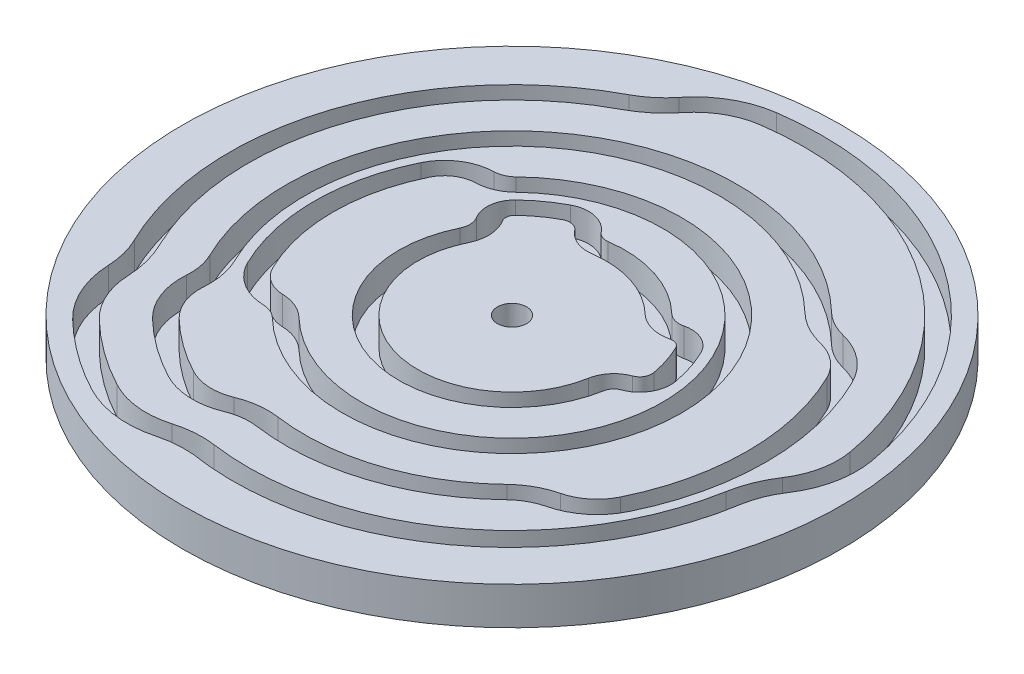
SolidWorks part; units mm, degrees
ref_plane "前视基准面" through (0, 0, 0) normal (0, 0, 1) x (1, 0, 0)
ref_plane "上视基准面" through (0, 0, 0) normal (0, 1, 0) x (1, 0, 0)
ref_plane "右视基准面" through (0, 0, 0) normal (1, 0, 0) x (0, 0, -1)
sketch "草图1" plane through (0, 0, 0) normal (0, 1, 0) x (1, 0, 0)
  line L0 (0, 0) -> (35, 0) construction
  line L1 (0, 0) -> (28.3156, -20.5725) construction
  line L2 (0, 0) -> (10.8156, -33.287) construction
  line L3 (0, 0) -> (-10.8156, -33.287) construction
  line L4 (0, 0) -> (-28.3156, -20.5725) construction
  line L5 (0, 0) -> (-35, 0) construction
  line L6 (0, 0) -> (-28.3156, 20.5725) construction
  line L7 (0, 0) -> (-10.8156, 33.287) construction
  line L8 (0, 0) -> (10.8156, 33.287) construction
  line L9 (0, 0) -> (28.3156, 20.5725) construction
  line L10 (0, 0) -> (34.4683, -6.0777) construction
  line L11 (0, 0) -> (14.7721, 2.6047) construction
  line L12 (0, 0) -> (10.4199, 10.7901) construction
  line L13 (0, 0) -> (13.4819, 6.5756) construction
  line L14 (0, 0) -> (-4.8711, 34.6594) construction
  line L15 (0, 0) -> (-7.0421, 13.2442) construction
  line L16 (0, 0) -> (-13.4819, 6.5756) construction
  line L17 (0, 0) -> (-10.4199, 10.7901) construction
  line L18 (-10.4199, 10.7901) -> (-24.313, 25.1769) construction
  line L19 (-13.4819, 6.5756) -> (-31.4578, 15.343) construction
  line L20 (-13.4819, -6.5756) -> (-31.4578, -15.343) construction
  line L21 (-10.4199, -10.7901) -> (-24.313, -25.1769) construction
  line L22 (0, 0) -> (-20.6079, -38.7578) construction
  line L23 (0, 0) -> (-5.3411, -38.0037) construction
  line L24 (0.985, -1.02) -> (31.4061, -32.522) construction
  line L25 (0, 0) -> (40.0534, -19.5353) construction
  circle A0 centre (0, 0) radius 35 construction
  circle A1 centre (0, 0) radius 10 construction
  circle A2 centre (0, 0) radius 15 construction
  circle A3 centre (0, 0) radius 12 construction
  arc A4 (12.8025, 2.2574) -> (11.6843, 5.6988) centre (0, 0) ccw
  arc A5 (9.8481, -1.7365) -> (11.9726, 0.8104) centre (13.1308, -2.3153) cw
  arc A6 (11.9726, 0.8104) -> (12.8025, 2.2574) centre (11.5202, 2.0313) ccw
  arc A7 (11.8177, -2.0838) -> (12.6675, -1.065) centre (13.1308, -2.3153) cw
  arc A8 (12.6675, -1.065) -> (14.7721, 2.6047) centre (11.5202, 2.0313) ccw
  circle A9 centre (0, 0) radius 13 construction
  arc A10 (13.4819, 6.5756) -> (14.7721, 2.6047) centre (0, 0) cw
  arc A11 (-1.3917, 9.9027) -> (-4.4704, 11.1362) centre (-1.8556, 13.2036) cw
  arc A12 (-4.4704, 11.1362) -> (-6.1031, 11.4783) centre (-5.4918, 10.3286) ccw
  arc A13 (6.9466, 7.1934) -> (10.6059, 6.2045) centre (9.6728, 10.0164) ccw
  arc A14 (8.3359, 8.6321) -> (10.1304, 8.1471) centre (9.6728, 10.0164) ccw
  arc A15 (10.1304, 8.1471) -> (13.4819, 6.5756) centre (10.8315, 5.2829) cw
  arc A16 (10.6059, 6.2045) -> (11.6843, 5.6988) centre (10.8315, 5.2829) cw
  arc A17 (-2.9016, 12.3766) -> (-7.0421, 13.2442) centre (-5.4918, 10.3286) ccw
  arc A18 (-1.6701, 11.8832) -> (-2.9016, 12.3766) centre (-1.8556, 13.2036) cw
  arc A19 (-1.3917, 9.9027) -> (6.9466, 7.1934) centre (0, 0) cw
  arc A20 (-1.6701, 11.8832) -> (8.3359, 8.6321) centre (0, 0) cw
  arc A21 (-6.1031, 11.4783) -> (-9.0306, 9.3514) centre (0, 0) ccw
  arc A22 (-10.4199, 10.7901) -> (-7.0421, 13.2442) centre (0, 0) cw
  arc A23 (-9.1782, 8.1695) -> (-9.0306, 9.3514) centre (-8.3714, 8.6689) cw
  arc A24 (-10.8788, 7.1169) -> (-10.4199, 10.7901) centre (-8.3714, 8.6689) cw
  arc A25 (-8.9879, 4.3837) -> (-9.1782, 8.1695) centre (-12.5152, 6.1041) ccw
  arc A26 (-10.7855, 5.2605) -> (-10.8788, 7.1169) centre (-12.5152, 6.1041) ccw
  arc A27 (-8.9879, 4.3837) -> (9.8481, -1.7365) centre (0, 0) ccw
  arc A28 (-10.7855, 5.2605) -> (11.8177, -2.0838) centre (0, 0) ccw
  circle A29 centre (0, 0) radius 16 construction
  circle A30 centre (0, 0) radius 18 construction
  circle A31 centre (0, 0) radius 19 construction
  circle A32 centre (0, 0) radius 21 construction
  arc A33 (-12.5039, 12.9481) -> (-14.1657, 12.2475) centre (-14.2408, 14.7467) cw
  arc A34 (-14.1657, 12.2475) -> (-18.8747, 9.2058) centre (-14.003, 6.8297) ccw
  arc A35 (-11.1145, 11.5094) -> (-14.1057, 10.2484) centre (-14.2408, 14.7467) cw
  arc A36 (-14.1057, 10.2484) -> (-17.0771, 8.3291) centre (-14.003, 6.8297) ccw
  arc A37 (-18.8747, -9.2058) -> (-18.8747, 9.2058) centre (0, 0) cw
  arc A38 (-17.0771, -8.3291) -> (-17.0771, 8.3291) centre (0, 0) cw
  arc A39 (-11.1145, -11.5094) -> (-11.1145, 11.5094) centre (0, 0) ccw
  arc A40 (-12.5039, -12.9481) -> (-12.5039, 12.9481) centre (0, 0) ccw
  arc A41 (-14.1057, -10.2484) -> (-17.0771, -8.3291) centre (-14.003, -6.8297) cw
  arc A42 (-11.1145, -11.5094) -> (-14.1057, -10.2484) centre (-14.2408, -14.7467) ccw
  arc A43 (-12.5039, -12.9481) -> (-14.1657, -12.2475) centre (-14.2408, -14.7467) ccw
  arc A44 (-14.1657, -12.2475) -> (-18.8747, -9.2058) centre (-14.003, -6.8297) cw
  arc A45 (-14.1057, -10.2484) -> (-13.1985, -13.6675) centre (-10.8226, -11.2072) ccw [skipped]
  arc A46 (-14.3807, -7.0139) -> (-14.1057, -10.2484) centre (-18.4256, -8.9868) cw [skipped]
  arc A47 (-16.1783, -7.8907) -> (-16.0255, -9.6877) centre (-18.4256, -8.9868) cw [skipped]
  arc A48 (-16.0255, -9.6877) -> (-14.5878, -15.1061) centre (-10.8226, -11.2072) ccw [skipped]
  circle A49 centre (0, 0) radius 22 construction
  circle A50 centre (0, 0) radius 24 construction
  circle A51 centre (0, 0) radius 25 construction
  circle A52 centre (0, 0) radius 27 construction
  arc A53 (24.2674, 11.836) -> (19.4142, 15.7508) centre (17.6639, 8.6153) ccw
  arc A54 (19.4142, 15.7508) -> (16.6718, 17.2642) centre (20.8456, 21.5862) cw
  arc A55 (22.4699, 10.9593) -> (18.9378, 13.8084) centre (17.6639, 8.6153) ccw
  arc A56 (18.9378, 13.8084) -> (15.2825, 15.8255) centre (20.8456, 21.5862) cw
  arc A57 (-6.4483, -24.1541) -> (-3.3402, -23.7664) centre (-4.1764, -29.7163) cw
  arc A58 (-7.2046, -22.3026) -> (-3.0618, -21.7859) centre (-4.1764, -29.7163) cw
  arc A59 (-12.6757, -23.8396) -> (-6.4483, -24.1541) centre (-9.2265, -17.3525) ccw
  arc A60 (-11.7368, -22.0737) -> (-7.2046, -22.3026) centre (-9.2265, -17.3525) ccw
  arc A61 (-20.9792, -13.5967) -> (-21.5711, -10.5209) centre (-26.9714, -13.1548) ccw
  arc A62 (-18.9847, -13.7438) -> (-19.7735, -9.6442) centre (-26.9714, -13.1548) ccw
  arc A63 (-18.7558, -19.4222) -> (-20.9792, -13.5967) centre (-13.6521, -14.1371) cw
  arc A64 (-17.3665, -17.9835) -> (-18.9847, -13.7438) centre (-13.6521, -14.1371) cw
  arc A65 (15.2825, -15.8255) -> (18.9378, -13.8084) centre (20.8456, -21.5862) cw
  arc A66 (18.9378, -13.8084) -> (22.4699, -10.9593) centre (17.6639, -8.6153) ccw
  arc A67 (19.4142, -15.7508) -> (16.6718, -17.2642) centre (20.8456, -21.5862) ccw
  arc A68 (24.2674, -11.836) -> (19.4142, -15.7508) centre (17.6639, -8.6153) cw
  arc A69 (-21.5711, -10.5209) -> (16.6718, 17.2642) centre (0, 0) cw
  arc A70 (-11.7368, -22.0737) -> (-17.3665, -17.9835) centre (0, 0) cw
  arc A71 (-12.6757, -23.8396) -> (-18.7558, -19.4222) centre (0, 0) cw
  arc A72 (15.2825, 15.8255) -> (-19.7735, -9.6442) centre (0, 0) ccw
  arc A73 (15.2825, -15.8255) -> (-3.0618, -21.7859) centre (0, 0) cw
  arc A74 (16.6718, -17.2642) -> (-3.3402, -23.7664) centre (0, 0) cw
  arc A75 (22.4699, -10.9593) -> (22.4699, 10.9593) centre (0, 0) ccw
  arc A76 (24.2674, -11.836) -> (24.2674, 11.836) centre (0, 0) ccw
  circle A77 centre (0, 0) radius 35
  circle A78 centre (0, 0) radius 30 construction
  circle A79 centre (0, 0) radius 28 construction
  circle A80 centre (0, 0) radius 31 construction
  circle A81 centre (0, 0) radius 33 construction
  arc A82 (27.5746, -4.8621) -> (29.2876, -0.5734) centre (38.7201, -6.8274) cw
  arc A83 (29.2876, -0.5734) -> (30.529, 5.3831) centre (22.4519, 3.9589) ccw
  arc A84 (29.5442, -5.2094) -> (30.9545, -1.6786) centre (38.7201, -6.8274) cw
  arc A85 (30.9545, -1.6786) -> (32.4987, 5.7304) centre (22.4519, 3.9589) ccw
  arc A86 (-13.1452, 24.7225) -> (-9.5957, 27.677) centre (-18.4584, 34.7153) ccw
  arc A87 (-9.5957, 27.677) -> (-4.3144, 30.6983) centre (-3.1729, 22.5764) cw
  arc A88 (-4.5927, 32.6788) -> (-11.1619, 28.9208) centre (-3.1729, 22.5764) ccw
  arc A89 (-11.1619, 28.9208) -> (-14.0841, 26.4884) centre (-18.4584, 34.7153) cw
  arc A90 (-25.1662, -12.2744) -> (-24.0312, -16.7509) centre (-35.3383, -17.2356) cw
  arc A91 (-24.0312, -16.7509) -> (-21.5344, -22.2995) centre (-15.837, -16.3997) ccw
  arc A92 (-26.0294, -16.8366) -> (-26.9638, -13.1511) centre (-35.3383, -17.2356) ccw
  arc A93 (-26.0294, -16.8366) -> (-22.9237, -23.7382) centre (-15.837, -16.3997) ccw
  arc A94 (-15.4926, -29.1373) -> (-7.7363, -30.0191) centre (-10.4958, -19.7398) ccw
  arc A95 (-7.7363, -30.0191) -> (-4.1764, -29.7163) centre (-5.1119, -39.7953) cw
  arc A96 (-14.5536, -27.3714) -> (-8.0585, -28.0323) centre (-10.4958, -19.7398) ccw
  arc A97 (-8.0585, -28.0323) -> (-3.8968, -27.7275) centre (-5.2721, -37.5129) cw
  arc A98 (-3.8968, -27.7275) -> (27.5746, -4.8621) centre (0, 0) ccw
  arc A99 (29.5442, -5.2094) -> (-4.1764, -29.7163) centre (0.4305, -0.6026) cw
  arc A100 (-14.5536, -27.3714) -> (-21.5344, -22.2995) centre (0, 0) cw
  arc A101 (-15.4926, -29.1373) -> (-22.9237, -23.7382) centre (0, 0) cw
  arc A102 (-25.1662, -12.2744) -> (-13.1452, 24.7225) centre (0, 0) cw
  arc A103 (-26.9638, -13.1511) -> (-14.0841, 26.4884) centre (0, 0) cw
  arc A104 (-4.5927, 32.6788) -> (32.4987, 5.7304) centre (0, 0) cw
  arc A105 (-4.3144, 30.6983) -> (30.529, 5.3831) centre (0, 0) cw
  text T0 "             1" font "汉仪长仿宋体" height 3.5
  text T1 "  2" font "汉仪长仿宋体" height 3.5
  text T2 "         3" font "汉仪长仿宋体" height 3.5
  text T3 "         4" font "汉仪长仿宋体" height 3.5
  text T4 "   5         " font "汉仪长仿宋体" height 3.5
  text T5 "6                "
  text T6 "7                 "
  text T7 "8                 "
  text T8 "9              \r\n\r\n\r\n\r\n" font "汉仪长仿宋体" height 3.5
  text T9 "0 "
  point P17 (0, 0)
  point P19 (9.8481, -1.7365)
  point P21 (12.8025, 2.2574)
  point P27 (11.8177, -2.0838)
  point P29 (14.7721, 2.6047)
  point P48 (0, 0)
  point P55 (0, 0)
  point P69 (0, 0)
  point P95 (0, 0)
  point P135 (0, 0)
  point P147 (0, 0)
  point P160 (-0.1247, 0.6846)
  dimension "D1" = 70
  dimension "D2" = 20
  dimension "D4" = 30
  dimension "D6" = 24
  dimension "D7" = 2
  dimension "D12" = 1
  dimension "D13" = 2
  dimension "D14" = 1
  dimension "D15" = 2
  dimension "D19" = 1
  dimension "D20" = 2
  dimension "D21" = 1
  dimension "D22" = 2
  dimension "D28" = 1
  dimension "D29" = 2
  dimension "D5" = 10
  dimension "D8" = 10
  dimension "D9" = 10
  dimension "D10" = 10
  dimension "D16" = 10
  dimension "D18" = 10
  dimension "D24" = 10
  dimension "D25" = 10
  dimension "D26" = 10
  dimension "D27" = 10
  dimension "1" = 1
  dimension "2" = 2
  dimension "D3" = 10
  dimension "D11" = 2
  dimension "D17" = 2
  dimension "D23" = 2
extrude "凸台-拉伸1" add sketch "草图1" along normal blind 3 contours A25 A27 A5 A6 A4 A16 A13 A19 A11 A12 A21 A23 | A42 A39 A35 A36 A38 A41 A28 A26 A24 A22 A17 A18 A20 A14 A15 A10 A8 A7 | A66 A75 A55 A56 A72 A62 A64 A70 A60 A58 A73 A65 A43 A44 A37 A34 A33 A40 | A105 A87 A86 A102 A90 A91 A100 A96 A97 A98 A82 A83 A76 A68 A67 A74 A57 A59 A71 A63 A61 A69 A54 A53 | A77 A88 A104 A85 A84 A99 A95 A94 A101 A93 A92 A103 A89
sketch "草图3" plane through (0, 0, 0) normal (0, -1, 0) x (1, 0, 0)
  circle A0 centre (0, 0) radius 35
extrude "凸台-拉伸2" add sketch "草图3" along normal blind 1
sketch "草图4" plane through (0, 3, 0) normal (0, 1, 0) x (1, 0, 0)
  circle A0 centre (0, 0) radius 1.55
  dimension "D1" = 3.1
extrude "切除-拉伸1" cut sketch "草图4" against normal through all
